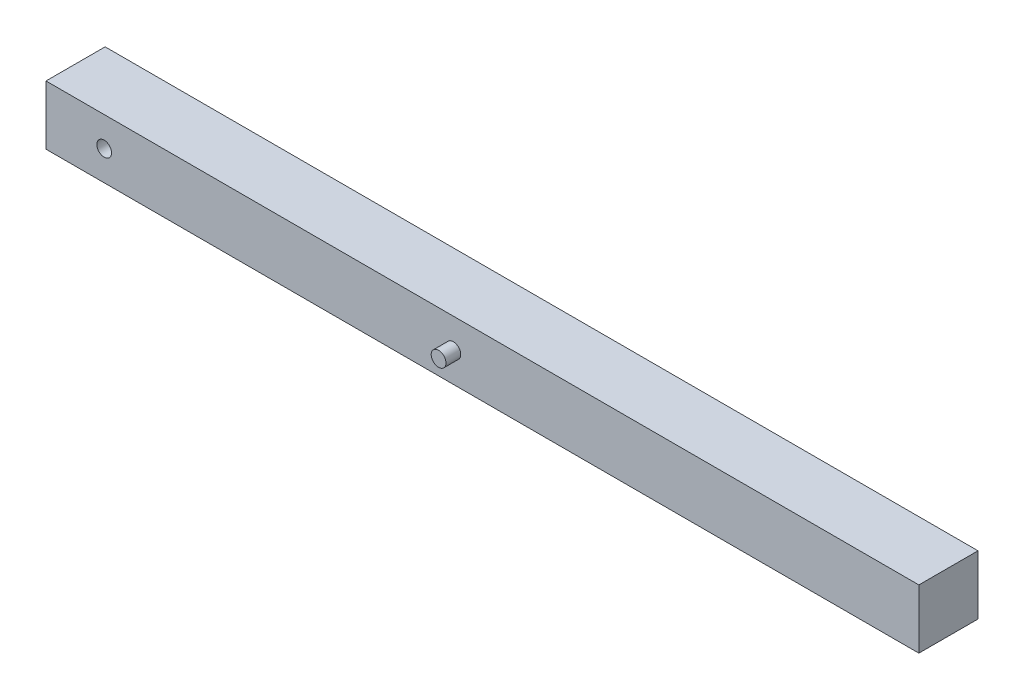
SolidWorks part; units mm, degrees
ref_plane "Front Plane" through (0, 0, 0) normal (0, 0, 1) x (1, 0, 0)
ref_plane "Top Plane" through (0, 0, 0) normal (0, 1, 0) x (1, 0, 0)
ref_plane "Right Plane" through (0, 0, 0) normal (1, 0, 0) x (0, 0, -1)
sketch "Sketch1" plane through (0, 0, 0) normal (0, 0, 1) x (1, 0, 0)
  line L0 (-39.3809, -16.3705) -> (710.6191, -16.3705) construction
  line L1 (-39.3809, 9.0295) -> (710.6191, 9.0295)
  line L2 (-39.3809, 9.0295) -> (-39.3809, -41.7705)
  line L3 (-39.3809, -41.7705) -> (710.6191, -41.7705)
  line L4 (710.6191, 9.0295) -> (710.6191, -41.7705)
  line L5 (10.6191, -10.0205) -> (10.6191, -22.7205) construction
  circle A0 centre (10.6191, -16.3705) radius 6.35
  dimension "D3" = 12.7
  dimension "D1" = 750
  dimension "D2" = 50.8
  dimension "D4" = 50
extrude "Boss-Extrude1" add sketch "Sketch1" along normal blind 50.8
sketch "Sketch2" plane through (0, 0, 50.8) normal (0, 0, 1) x (1, 0, 0)
  line L0 (-39.3809, 9.0295) -> (-39.3809, -41.7705) construction
  circle A0 centre (310.6191, -16.3705) radius 6.35
  circle A1 centre (10.6191, -16.3705) radius 6.35 construction
  dimension "D1" = 12.7
  dimension "D2" = 350
  dimension "D3" = 0
extrude "Boss-Extrude2" add sketch "Sketch2" along normal blind 12.7
